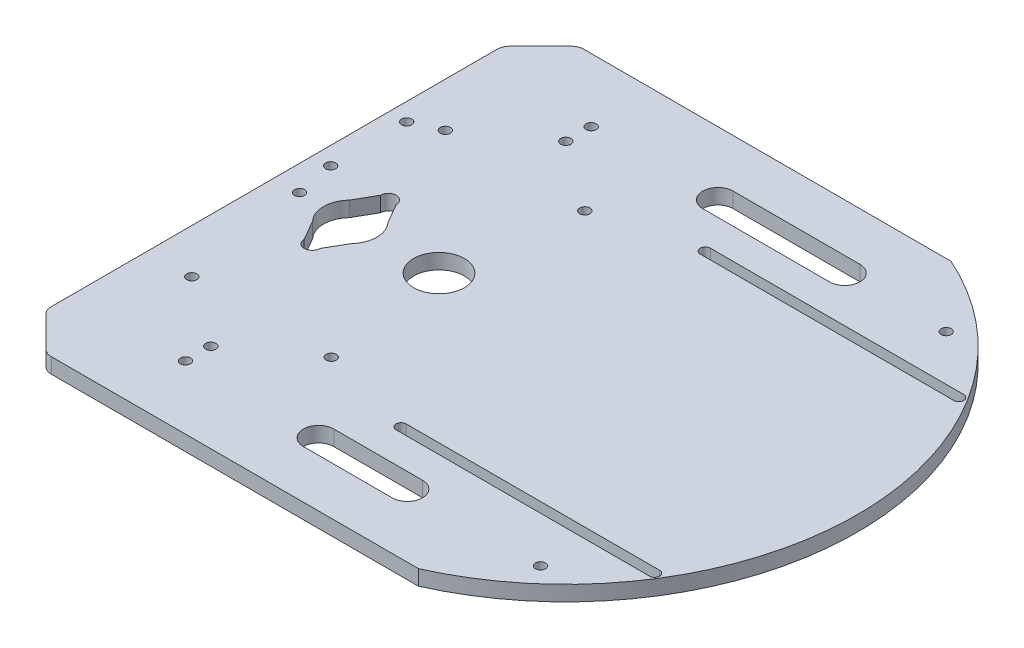
SolidWorks part; units mm, degrees
ref_plane "Front Plane" through (0, 0, 0) normal (0, 0, 1) x (1, 0, 0)
ref_plane "Top Plane" through (0, 0, 0) normal (0, 1, 0) x (1, 0, 0)
ref_plane "Right Plane" through (0, 0, 0) normal (1, 0, 0) x (0, 0, -1)
sketch "Sketch1" plane through (0, 0, 0) normal (0, 1, 0) x (1, 0, 0)
  line L1 (-46.9042, -105) -> (46.9042, -105)
  line L2 (-46.9042, 105) -> (46.9042, 105)
  line L7 (-70, 0) -> (70, 0) construction
  line L8 (-70, 80) -> (70, 80) construction
  line L9 (-70, 80) -> (-70, -80) construction
  line L10 (-70, -80) -> (70, -80) construction
  line L11 (70, 80) -> (70, -80) construction
  circle A0 centre (-70, 80) radius 2
  circle A1 centre (70, 80) radius 2
  circle A2 centre (70, -80) radius 2
  circle A3 centre (-70, -80) radius 2
  circle A4 centre (-85, 0) radius 10.5
  arc A8 (-46.9042, 105) -> (-46.9042, -105) centre (0, 0) ccw
  arc A9 (46.9042, -105) -> (46.9042, 105) centre (0, 0) ccw
  point P0 (0, 0)
  point P13 (0, 0)
  dimension "D1" = 105
  dimension "D8" = 230
  dimension "D5" = 4
  dimension "D6" = 21
  dimension "D2" = 140
  dimension "D3" = 160
  dimension "D4" = 105
  dimension "D7" = 85
  dimension "D9" = 105
extrude "Boss-Extrude1" add sketch "Sketch1" along normal blind 6
sketch "Sketch2" plane through (0, 0, 0) normal (0, -1, 0) x (1, 0, 0)
  line L0 (-95.5, 0) -> (-74.5, 0) construction
  line L1 (-85, 18.1537) -> (-85, -10.5) construction
  line L2 (-88.1537, 15) -> (-92.6802, 7.1599)
  line L3 (-81.8463, -15) -> (-77.3198, -7.1599)
  line L4 (-81.8463, 15) -> (-77.3198, 7.1599)
  line L5 (-88.1537, -15) -> (-92.6802, -7.1599)
  line L6 (-20, -80) -> (30, -80) construction
  line L7 (-20, -74) -> (30, -74)
  line L8 (-20, -86) -> (30, -86)
  line L9 (17.5, 80) -> (-17.5, 80) construction
  line L10 (17.5, 74) -> (-17.5, 74)
  line L11 (17.5, 86) -> (-17.5, 86)
  circle A0 centre (-85, 0) radius 10.5 construction
  arc A1 (-92.6802, 7.1599) -> (-92.6802, -7.1599) centre (-85, 0) ccw
  arc A2 (-81.8463, 15) -> (-88.1537, 15) centre (-85, 15) ccw
  arc A3 (-81.8463, -15) -> (-88.1537, -15) centre (-85, -15) cw
  arc A4 (-77.3198, -7.1599) -> (-77.3198, 7.1599) centre (-85, 0) ccw
  circle A5 centre (-50, 0) radius 10
  arc A6 (-20, -74) -> (-20, -86) centre (-20, -80) ccw
  arc A7 (30, -86) -> (30, -74) centre (30, -80) ccw
  arc A8 (17.5, 74) -> (17.5, 86) centre (17.5, 80) ccw
  arc A9 (-17.5, 86) -> (-17.5, 74) centre (-17.5, 80) ccw
  circle A10 centre (-105, 0) radius 2
  arc A11 (-46.9042, 105) -> (-46.9042, -105) centre (0, 0) ccw construction
  point P20 (5, -80)
  point P28 (0, 80)
  point P35 (-115, 0)
  dimension "D2" = 6.3075
  dimension "D3" = 30
  dimension "D5" = 20
  dimension "D8" = 6
  dimension "D11" = 6
  dimension "D15" = 4
  dimension "D1" = 15
  dimension "D4" = 30
  dimension "D6" = 35
  dimension "D7" = 50
  dimension "D9" = 80
  dimension "D10" = 90
  dimension "D12" = 35
  dimension "D13" = 80
  dimension "D14" = 10
extrude "Cut-Extrude2" cut sketch "Sketch2" against normal blind 19
ref_plane "Plane1" through (0, 0, 0) normal (0, -1, 0) x (-1, 0, 0)
sketch "Sketch3" plane through (0, 0, 0) normal (0, -1, 0) x (-1, 0, 0)
  line L0 (46.9042, -105) -> (115, -105)
  line L1 (46.9042, 105) -> (115, 105)
  line L2 (115, 105) -> (115, -105)
  arc A1 (46.9042, -105) -> (46.9042, 105) centre (0, 0) ccw construction
  arc A2 (46.9042, -105) -> (46.9042, 105) centre (0, 0) ccw
  dimension "D1" = 68.0958
extrude "Boss-Extrude2" add sketch "Sketch3" against normal blind 6 contours A2 L0 L2 | A2 L2 L1
chamfer "Chamfer1" distance 15 angle 45 2 edges at (-115, 3, -105) (-115, 3, 105)
fillet "Fillet1" radius 5 4 edges at (-100, 3, -105) (-115, 3, -90) (-100, 3, 105) (-115, 3, 90)
sketch "Sketch4" plane through (0, 6, 0) normal (0, 1, 0) x (1, 0, 0)
  line L0 (0, 0) -> (-155.0567, 0) construction
  line L1 (-42.5, -50) -> (-97.5, -50) construction
  line L2 (-42.5, -50) -> (-42.5, 50) construction
  line L3 (-42.5, 50) -> (-97.5, 50) construction
  line L4 (-97.5, -50) -> (-97.5, 50) construction
  line L5 (-42.5, -50) -> (-97.5, 50) construction
  line L6 (-42.5, 50) -> (-97.5, -50) construction
  line L7 (-115, 87.9289) -> (-115, -87.9289) construction
  line L8 (-70, 0) -> (-70, -70) construction
  line L9 (-70, 0) -> (-70, 70) construction
  line L13 (30, 86) -> (-20, 86) construction
  circle A0 centre (-42.5, -50) radius 2
  circle A1 centre (-97.5, -50) radius 2
  circle A2 centre (-97.5, 50) radius 2
  circle A3 centre (-42.5, 50) radius 2
  circle A4 centre (-70, 70) radius 2
  circle A5 centre (-70, -70) radius 2
  circle A6 centre (-108, 15.2593) radius 2
  circle A7 centre (-108, 45.2593) radius 2
  point P0 (-70, 0)
  dimension "D1" = 4
  dimension "D2" = 4
  dimension "D3" = 4
  dimension "D4" = 4
  dimension "D10" = 4
  dimension "D11" = 4
  dimension "D12" = 4
  dimension "D13" = 4
  dimension "D5" = 100
  dimension "D6" = 55
  dimension "D7" = 45
  dimension "D8" = 70
  dimension "D9" = 70
  dimension "D14" = 30
  dimension "D15" = 38
extrude "Cut-Extrude3" cut sketch "Sketch4" against normal blind 10
sketch "Sketch5" plane through (0, 6, 0) normal (0, 1, 0) x (1, 0, 0)
  line L0 (-123.2487, 0) -> (143.3498, 0) construction
  line L1 (-123.2487, -50) -> (143.3498, -50) construction
  line L2 (-123.2487, 60) -> (143.3498, 60) construction
  line L3 (-5, 60) -> (95, 60) construction
  line L4 (-5, 62) -> (95, 62)
  line L5 (-5, 58) -> (95, 58)
  line L6 (-5, -60) -> (95, -60) construction
  line L7 (-5, -62) -> (95, -62)
  line L8 (-5, -58) -> (95, -58)
  arc A0 (-5, 62) -> (-5, 58) centre (-5, 60) ccw
  arc A1 (95, 58) -> (95, 62) centre (95, 60) ccw
  arc A2 (-5, -62) -> (-5, -58) centre (-5, -60) cw
  arc A3 (95, -58) -> (95, -62) centre (95, -60) cw
  point P9 (45, 60)
  point P16 (45, -60)
  dimension "D3" = 2
  dimension "D1" = 50
  dimension "D4" = 100
  dimension "D5" = 95
  dimension "D2" = 60
extrude "Cut-Extrude4" cut sketch "Sketch5" against normal blind 10
